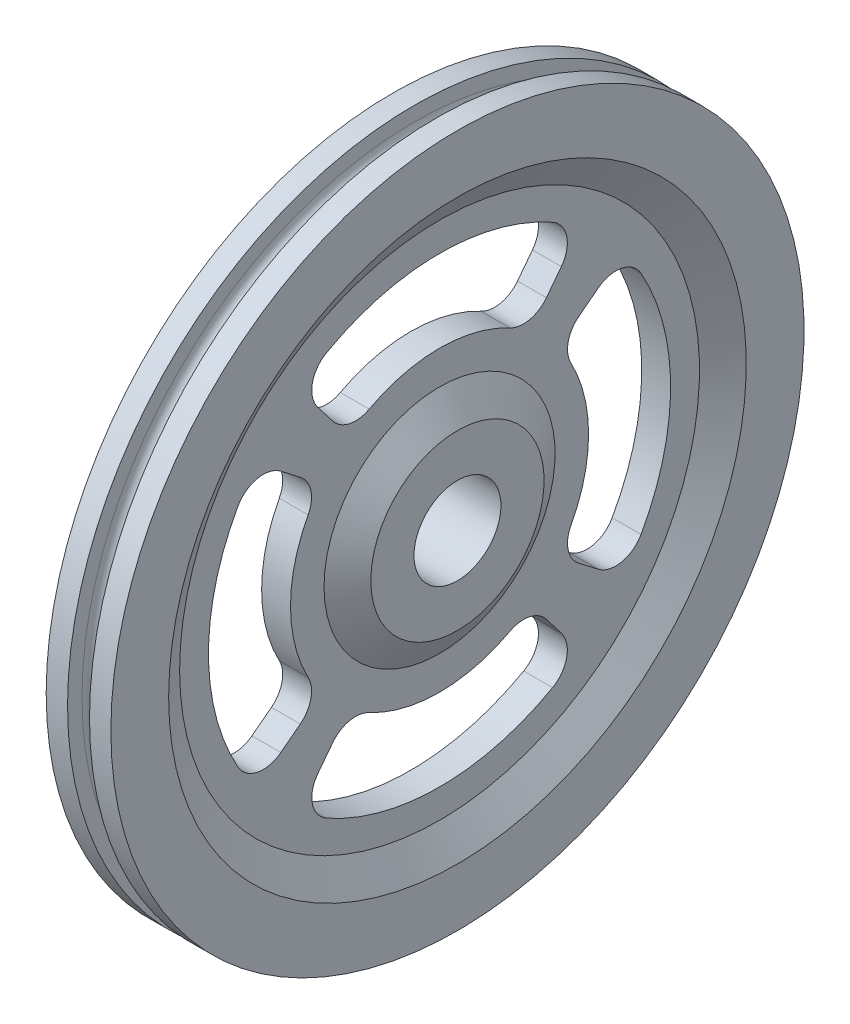
SolidWorks part; units mm, degrees
material "Plain Carbon Steel"
ref_plane "Front Plane" through (0, 0, 0) normal (0, 0, 1) x (1, 0, 0)
ref_plane "Top Plane" through (0, 0, 0) normal (0, 1, 0) x (1, 0, 0)
ref_plane "Right Plane" through (0, 0, 0) normal (1, 0, 0) x (0, 0, -1)
sketch "Sketch1" plane through (0, 0, 0) normal (0, 0, 1) x (1, 0, 0)
  line L3 (-7.112, 19.05) -> (-3.175, 25.4)
  line L4 (-3.175, 25.4) -> (-3.175, 57.15)
  line L5 (-3.175, 57.15) -> (-7.112, 63.5)
  line L6 (-7.112, 63.5) -> (-7.112, 76.2)
  line L7 (-7.112, 76.2) -> (-2.413, 76.2)
  line L8 (7.112, 76.2) -> (7.112, 63.5)
  line L9 (7.112, 63.5) -> (3.175, 57.15)
  line L10 (3.175, 57.15) -> (3.175, 25.4)
  line L11 (3.175, 25.4) -> (7.112, 19.05)
  line L16 (-7.112, 19.05) -> (-7.112, 9.5567)
  line L17 (-7.112, 9.5567) -> (7.112, 9.5567)
  line L18 (7.112, 9.5567) -> (7.112, 19.05)
  line L19 (-2.413, 73.025) -> (-2.413, 76.2)
  line L20 (2.413, 73.025) -> (2.413, 76.2)
  line L21 (2.413, 76.2) -> (7.112, 76.2)
  line L22 (0, 0) -> (7.112, 0) construction
  arc A0 (-2.413, 73.025) -> (2.413, 73.025) centre (0, 73.025) ccw
  point P1 (0, 9.5567)
  dimension "D11" = 4.826
  dimension "D1" = 14.224
  dimension "D2" = 9.5567
  dimension "D3" = 19.05
  dimension "D4" = 25.4
  dimension "D5" = 57.15
  dimension "D6" = 63.5
  dimension "D7" = 76.2
  dimension "D8" = 6.35
  dimension "D9" = 3.175
  dimension "D10" = 14.224
  dimension "D12" = 73.025
revolve "Revolve1" add sketch "Sketch1" angle 360 about L22
sketch "Sketch2" plane through (3.175, 0, 0) normal (1, 0, 0) x (0, 0, -1)
  line L0 (0, 32.766) -> (0, 50.8) construction
  line L1 (23.4964, 30.6212) -> (26.7819, 34.9029)
  line L2 (-23.4964, 30.6212) -> (-26.7819, 34.9029)
  arc A0 (24.8504, 44.3068) -> (-24.8504, 44.3068) centre (0, 0) ccw
  arc A1 (15.4621, 28.8883) -> (-15.4621, 28.8883) centre (0, 0) ccw
  arc A2 (26.7819, 34.9029) -> (24.8504, 44.3068) centre (21.7441, 38.7685) ccw
  arc A3 (15.4621, 28.8883) -> (23.4964, 30.6212) centre (18.4587, 34.4868) ccw
  arc A4 (-15.4621, 28.8883) -> (-23.4964, 30.6212) centre (-18.4587, 34.4868) cw
  arc A5 (-26.7819, 34.9029) -> (-24.8504, 44.3068) centre (-21.7441, 38.7685) cw
  dimension "D1" = 101.6
  dimension "D2" = 65.532
  dimension "D5" = 6.35
  dimension "D3" = 37.5
  dimension "D4" = 75
extrude "Cut-Extrude1" cut sketch "Sketch2" against normal up to next (6.35 mm away)
pattern_circular "CirPattern1" count 4 over 360 about axis through (0, 0, 0) along (1, 0, 0) of "Cut-Extrude1"
